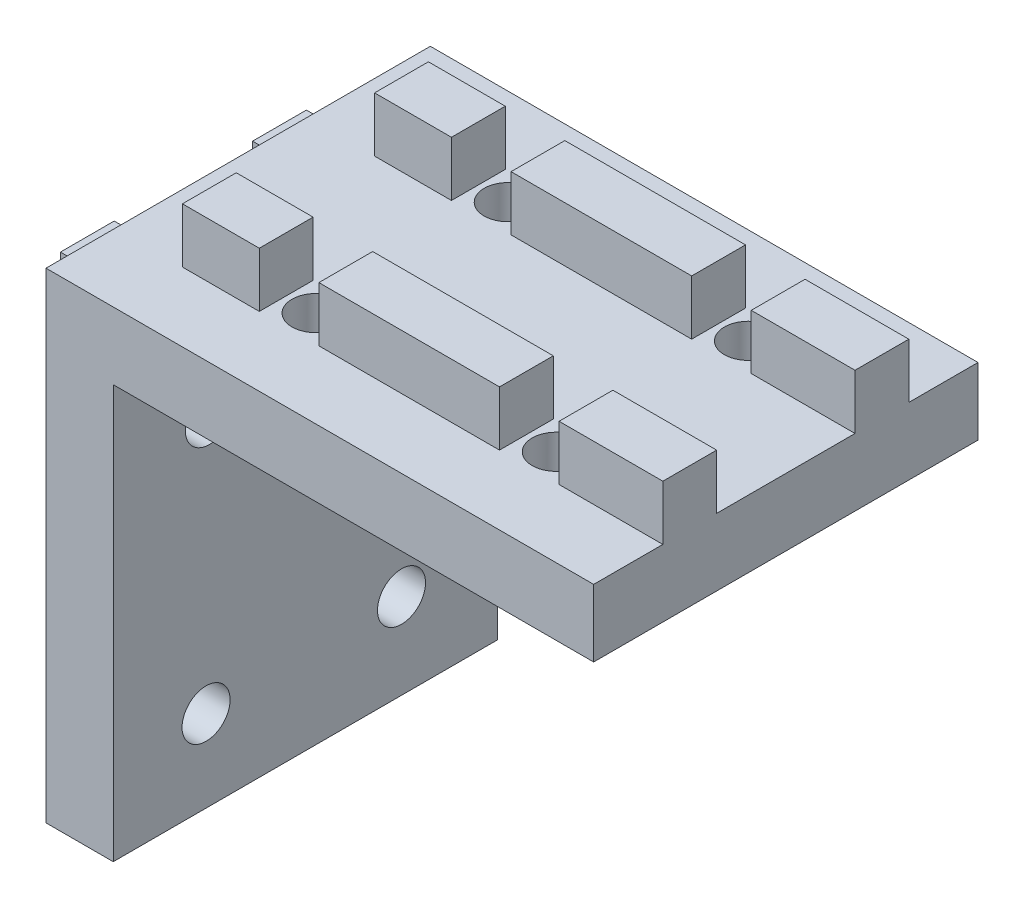
SolidWorks part; units mm, degrees
ref_plane "Alzado" through (0, 0, 0) normal (0, 0, 1) x (1, 0, 0)
ref_plane "Planta" through (0, 0, 0) normal (0, 1, 0) x (1, 0, 0)
ref_plane "Vista lateral" through (0, 0, 0) normal (1, 0, 0) x (0, 0, -1)
sketch "Croquis1" plane through (0, 0, 0) normal (0, 1, 0) x (1, 0, 0)
  line L1 (25, 20) -> (-25, 20)
  line L2 (25, 20) -> (25, -20)
  line L3 (25, -20) -> (-25, -20)
  line L4 (-25, 20) -> (-25, -20)
  line L5 (25, 20) -> (-25, -20) construction
  line L6 (25, -20) -> (-25, 20) construction
  point P0 (0, 0)
  dimension "D1" = 40
  dimension "D2" = 50
extrude "Saliente-Extruir1" add sketch "Croquis1" along normal blind 7
sketch "Croquis3" plane through (-25, 0, 0) normal (-1, 0, 0) x (0, 0, 1)
  line L0 (-20, 7) -> (20, 7) construction
  line L5 (-12.8, 12.7) -> (-7.2, 7) construction
  line L6 (7.2, 7) -> (12.8, 7)
  line L7 (7.2, 7) -> (7.2, 12.7)
  line L8 (7.2, 12.7) -> (12.8, 12.7)
  line L9 (12.8, 7) -> (12.8, 12.7)
  line L12 (-7.2, 7) -> (-12.8, 7)
  line L13 (-7.2, 7) -> (-7.2, 12.7)
  line L14 (-7.2, 12.7) -> (-12.8, 12.7)
  line L15 (-12.8, 7) -> (-12.8, 12.7)
  line L16 (-7.2, 12.7) -> (-12.8, 7) construction
  line L17 (7.2, 12.7) -> (12.8, 7) construction
  line L18 (12.8, 12.7) -> (7.2, 7) construction
  point P10 (-10, 9.85)
  point P11 (10, 9.85)
  dimension "D1" = 10
  dimension "D2" = 10
  dimension "D3" = 5.6
  dimension "D4" = 5.6
  dimension "D5" = 5.7
extrude "Saliente-Extruir3" add sketch "Croquis3" against normal up to surface (50 mm away) up to face at (25, 3.5, 0)
sketch "Croquis9" plane through (-25, 0, 0) normal (-1, 0, 0) x (0, 0, 1)
  line L0 (20, 7) -> (20, 0) construction
  line L1 (20, 7) -> (-20, 7)
  line L2 (20, 7) -> (20, -43)
  line L3 (20, -43) -> (-20, -43)
  line L4 (-20, 7) -> (-20, -43)
  line L5 (-20, 7) -> (-20, 0) construction
  line L6 (-7.2, 7) -> (7.2, 7) construction
  dimension "D1" = 50
extrude "Saliente-Extruir8" add sketch "Croquis9" along normal blind 7
sketch "Croquis10" plane through (0, -43, 0) normal (0, -1, 0) x (1, 0, 0)
  line L5 (-32, -20) -> (-32, 20) construction
  line L6 (-37.7, 12.8) -> (-32, 12.8)
  line L7 (-37.7, 12.8) -> (-37.7, 7.2)
  line L8 (-37.7, 7.2) -> (-32, 7.2)
  line L9 (-32, 12.8) -> (-32, 7.2)
  line L10 (-37.7, 12.8) -> (-32, 7.2) construction
  line L11 (-37.7, 7.2) -> (-32, 12.8) construction
  line L12 (-32, -7.2) -> (-37.7, -7.2)
  line L13 (-32, -7.2) -> (-32, -12.8)
  line L14 (-32, -12.8) -> (-37.7, -12.8)
  line L15 (-37.7, -7.2) -> (-37.7, -12.8)
  line L16 (-32, -7.2) -> (-37.7, -12.8) construction
  line L17 (-32, -12.8) -> (-37.7, -7.2) construction
  line L18 (-32, -20) -> (-25, -20) construction
  point P0 (-34.85, 10)
  point P5 (-34.85, -10)
  dimension "D1" = 10
  dimension "D2" = 10
  dimension "D3" = 5.6
  dimension "D4" = 5.6
  dimension "D6" = 5.7
extrude "Saliente-Extruir9" add sketch "Croquis10" against normal blind 45
sketch "Croquis18" plane through (-37.7, 0, 0) normal (-1, 0, 0) x (0, 0, 1)
  line L0 (-20, 7) -> (-20, -43) construction
  line L1 (-20, -37.2) -> (20, -37.2)
  line L2 (-20, -37.2) -> (-20, -31)
  line L3 (-20, -31) -> (20, -31)
  line L4 (20, -37.2) -> (20, -31)
  line L5 (-20, -37.2) -> (20, -31) construction
  line L6 (-20, -31) -> (20, -37.2) construction
  line L7 (20, -43) -> (20, 7) construction
  line L8 (12.8, -43) -> (20, -43) construction
  line L10 (20, -4.8) -> (-20, -4.8)
  line L11 (20, -4.8) -> (20, -11)
  line L12 (20, -11) -> (-20, -11)
  line L13 (-20, -4.8) -> (-20, -11)
  line L14 (20, -4.8) -> (-20, -11) construction
  line L15 (20, -11) -> (-20, -4.8) construction
  point P0 (0, -34.1)
  point P11 (0, -7.9)
  dimension "D1" = 6.2
  dimension "D2" = 12
  dimension "D3" = 6.2
  dimension "D4" = 32
extrude "Cortar-Extruir4" cut sketch "Croquis18" against normal up to surface (5.7 mm away) up to face at (-32, -19.6667, 0)
sketch "Croquis19" plane through (0, 12.7, 0) normal (0, 1, 0) x (1, 0, 0)
  line L0 (25, 20) -> (-32, 20) construction
  line L1 (-10.8, 20) -> (-17, 20)
  line L2 (-10.8, 20) -> (-10.8, -20)
  line L3 (-10.8, -20) -> (-17, -20)
  line L4 (-17, 20) -> (-17, -20)
  line L5 (-10.8, 20) -> (-17, -20) construction
  line L6 (-10.8, -20) -> (-17, 20) construction
  line L7 (14.2, 20) -> (8, 20)
  line L8 (14.2, 20) -> (14.2, -20)
  line L9 (14.2, -20) -> (8, -20)
  line L10 (8, 20) -> (8, -20)
  line L11 (14.2, 20) -> (8, -20) construction
  line L12 (14.2, -20) -> (8, 20) construction
  line L13 (-32, -20) -> (25, -20) construction
  line L14 (-32, -20) -> (-32, 20) construction
  point P0 (-13.9, 0)
  point P5 (11.1, 0)
  dimension "D1" = 6.2
  dimension "D2" = 15
  dimension "D3" = 40
  dimension "D4" = 6.2
extrude "Cortar-Extruir5" cut sketch "Croquis19" against normal up to surface (5.7 mm away) up to face at (-1.1667, 7, 0)
sketch "Croquis20" plane through (0, 7, 0) normal (0, 1, 0) x (1, 0, 0)
  line L0 (-17, 12.8) -> (-10.8, 7.2) construction
  line L1 (-10.8, 7.2) -> (-10.8, 12.8) construction
  line L2 (-10.8, 12.8) -> (-17, 7.2) construction
  line L3 (8, 12.8) -> (14.2, 7.2) construction
  line L4 (14.2, 12.8) -> (8, 7.2) construction
  line L5 (14.2, -12.8) -> (8, -7.2) construction
  line L6 (8, -12.8) -> (14.2, -7.2) construction
  line L7 (-17, -7.2) -> (-10.8, -12.8) construction
  line L8 (-10.8, -7.2) -> (-17, -12.8) construction
  circle A0 centre (-13.9, 10) radius 2.5
  circle A1 centre (11.1, 10) radius 2.5
  circle A2 centre (11.1, -10) radius 2.5
  circle A3 centre (-13.9, -10) radius 2.5
  dimension "D1" = 5
extrude "Cortar-Extruir6" cut sketch "Croquis20" against normal up to surface (7 mm away) up to face at (0, 0, 0)
sketch "Croquis21" plane through (-32, 0, 0) normal (-1, 0, 0) x (0, 0, 1)
  line L0 (-12.8, -4.8) -> (-7.2, -11) construction
  line L1 (-7.2, -4.8) -> (-12.8, -11) construction
  line L2 (7.2, -4.8) -> (12.8, -11) construction
  line L3 (12.8, -4.8) -> (7.2, -11) construction
  line L4 (-12.8, -31) -> (-7.2, -37.2) construction
  line L5 (-7.2, -31) -> (-12.8, -37.2) construction
  line L6 (7.2, -31) -> (12.8, -37.2) construction
  line L7 (7.2, -37.2) -> (12.8, -31) construction
  circle A0 centre (-10, -7.9) radius 2.5
  circle A1 centre (10, -7.9) radius 2.5
  circle A2 centre (10.3394, -34.4758) radius 2.5
  circle A3 centre (-10, -34.1) radius 2.5
  dimension "D1" = 5
extrude "Cortar-Extruir7" cut sketch "Croquis21" against normal up to surface (7 mm away) up to face at (-25, -21.5, 0)
